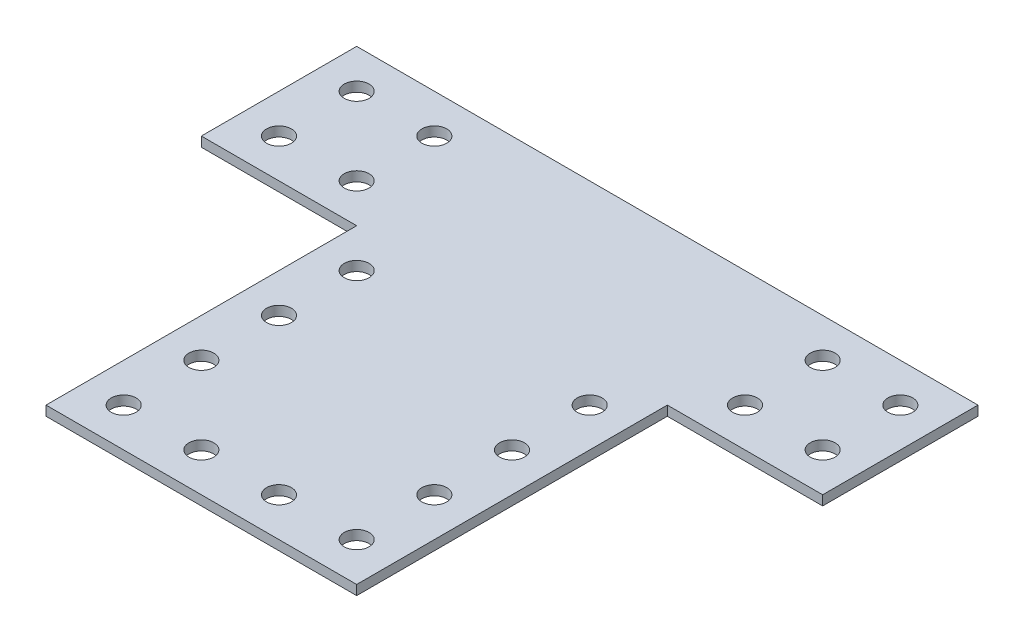
SolidWorks part; units mm, degrees
material "1060 Alloy"
ref_plane "Front Plane" through (0, 0, 0) normal (0, 0, 1) x (1, 0, 0)
ref_plane "Top Plane" through (0, 0, 0) normal (0, 1, 0) x (1, 0, 0)
ref_plane "Right Plane" through (0, 0, 0) normal (1, 0, 0) x (0, 0, -1)
sketch "Sketch3" plane through (0, 0, 0) normal (0, 1, 0) x (1, 0, 0)
  line L0 (0, 0) -> (101.6, 0)
  line L1 (101.6, 0) -> (101.6, -25.4)
  line L2 (101.6, -25.4) -> (76.2, -25.4)
  line L3 (76.2, -25.4) -> (76.2, -76.2)
  line L4 (76.2, -76.2) -> (25.4, -76.2)
  line L5 (25.4, -76.2) -> (25.4, -25.4)
  line L6 (25.4, -25.4) -> (0, -25.4)
  line L7 (0, -25.4) -> (0, 0)
  dimension "D1" = 50.8
  dimension "D2" = 25.4
  dimension "D3" = 50.8
  dimension "D4" = 25.4
  dimension "D5" = 101.6
extrude "Boss-Extrude1" add sketch "Sketch3" along normal blind 1.5875
sketch "Sketch4" plane through (0, 1.5875, 0) normal (0, 1, 0) x (1, 0, 0)
  line L0 (101.6, 0) -> (0, 0) construction
  line L1 (0, 0) -> (0, -25.4) construction
  circle A0 centre (6.35, -6.35) radius 2.032
  circle A1 centre (19.05, -6.35) radius 2.032
  circle A6 centre (82.55, -6.35) radius 2.032
  circle A7 centre (95.25, -6.35) radius 2.032
  circle A8 centre (107.95, -6.35) radius 2.032
  circle A9 centre (120.65, -6.35) radius 2.032
  circle A10 centre (133.35, -6.35) radius 2.032
  circle A11 centre (146.05, -6.35) radius 2.032
  circle A12 centre (19.05, -19.05) radius 2.032
  circle A17 centre (82.55, -19.05) radius 2.032
  circle A18 centre (95.25, -19.05) radius 2.032
  circle A19 centre (107.95, -19.05) radius 2.032
  circle A20 centre (120.65, -19.05) radius 2.032
  circle A21 centre (133.35, -19.05) radius 2.032
  circle A22 centre (146.05, -19.05) radius 2.032
  circle A23 centre (19.05, -31.75) radius 2.032
  circle A24 centre (31.75, -31.75) radius 2.032
  circle A27 centre (69.85, -31.75) radius 2.032
  circle A28 centre (82.55, -31.75) radius 2.032
  circle A29 centre (95.25, -31.75) radius 2.032
  circle A30 centre (107.95, -31.75) radius 2.032
  circle A31 centre (120.65, -31.75) radius 2.032
  circle A32 centre (133.35, -31.75) radius 2.032
  circle A33 centre (146.05, -31.75) radius 2.032
  circle A34 centre (19.05, -44.45) radius 2.032
  circle A35 centre (31.75, -44.45) radius 2.032
  circle A38 centre (69.85, -44.45) radius 2.032
  circle A39 centre (82.55, -44.45) radius 2.032
  circle A40 centre (95.25, -44.45) radius 2.032
  circle A41 centre (107.95, -44.45) radius 2.032
  circle A42 centre (120.65, -44.45) radius 2.032
  circle A43 centre (133.35, -44.45) radius 2.032
  circle A44 centre (146.05, -44.45) radius 2.032
  circle A45 centre (19.05, -57.15) radius 2.032
  circle A46 centre (31.75, -57.15) radius 2.032
  circle A49 centre (69.85, -57.15) radius 2.032
  circle A50 centre (82.55, -57.15) radius 2.032
  circle A51 centre (95.25, -57.15) radius 2.032
  circle A52 centre (107.95, -57.15) radius 2.032
  circle A53 centre (120.65, -57.15) radius 2.032
  circle A54 centre (133.35, -57.15) radius 2.032
  circle A55 centre (146.05, -57.15) radius 2.032
  circle A56 centre (19.05, -69.85) radius 2.032
  circle A57 centre (31.75, -69.85) radius 2.032
  circle A58 centre (44.45, -69.85) radius 2.032
  circle A59 centre (57.15, -69.85) radius 2.032
  circle A60 centre (69.85, -69.85) radius 2.032
  circle A61 centre (82.55, -69.85) radius 2.032
  circle A62 centre (95.25, -69.85) radius 2.032
  circle A63 centre (107.95, -69.85) radius 2.032
  circle A64 centre (120.65, -69.85) radius 2.032
  circle A65 centre (133.35, -69.85) radius 2.032
  circle A66 centre (146.05, -69.85) radius 2.032
  circle A67 centre (6.35, -19.05) radius 2.032
  circle A68 centre (6.35, -31.75) radius 2.032
  circle A69 centre (6.35, -44.45) radius 2.032
  circle A70 centre (6.35, -57.15) radius 2.032
  circle A71 centre (6.35, -69.85) radius 2.032
  circle A72 centre (44.45, -57.15) radius 2.032 [skipped]
  circle A73 centre (57.15, -57.15) radius 2.032 [skipped]
  circle A74 centre (44.45, -44.45) radius 2.032 [skipped]
  circle A75 centre (57.15, -44.45) radius 2.032 [skipped]
  circle A76 centre (57.15, -31.75) radius 2.032 [skipped]
  circle A77 centre (44.45, -31.75) radius 2.032 [skipped]
  circle A78 centre (44.45, -19.05) radius 2.032 [skipped]
  circle A79 centre (57.15, -19.05) radius 2.032 [skipped]
  circle A80 centre (57.15, -6.35) radius 2.032 [skipped]
  circle A81 centre (44.45, -6.35) radius 2.032 [skipped]
  circle A82 centre (31.75, -19.05) radius 2.032 [skipped]
  circle A83 centre (69.85, -6.35) radius 2.032 [skipped]
  circle A84 centre (31.75, -6.35) radius 2.032 [skipped]
  circle A85 centre (69.85, -19.05) radius 2.032 [skipped]
  dimension "D1" = 4.064
  dimension "D2" = 6.35
  dimension "D3" = 6.35
  dimension "D4" = 12
  dimension "D5" = 6
extrude "Cut-Extrude1" cut sketch "Sketch4" against normal blind 1.5875
